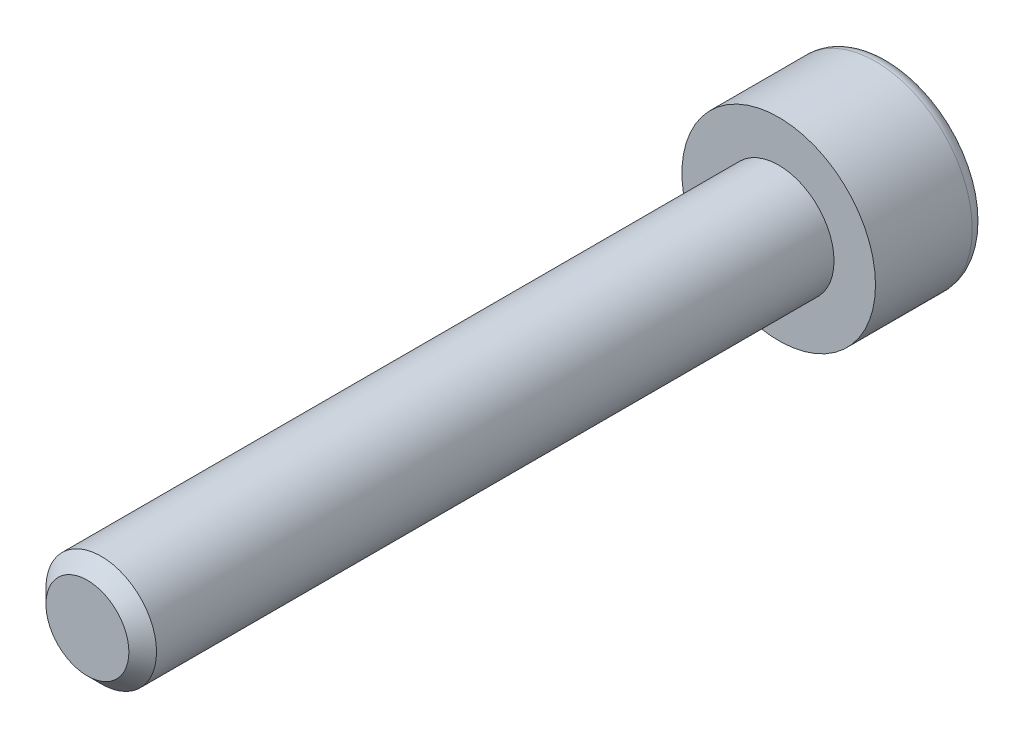
SolidWorks part; units mm, degrees
ref_plane "Plan de face" through (0, 0, 0) normal (0, 0, 1) x (1, 0, 0)
ref_plane "Plan de dessus" through (0, 0, 0) normal (0, 1, 0) x (1, 0, 0)
ref_plane "Plan de droite" through (0, 0, 0) normal (1, 0, 0) x (0, 0, -1)
sketch "Esquisse1" plane through (0, 0, 0) normal (0, 0, 1) x (1, 0, 0)
  circle A0 centre (0, 0) radius 3.5
  dimension "D1" = 7
extrude "Boss.-Extru.1" add sketch "Esquisse1" along normal blind 4
sketch "Esquisse2" plane through (0, 0, 4) normal (0, 0, 1) x (1, 0, 0)
  circle A0 centre (0, 0) radius 2
  dimension "D1" = 4
extrude "Boss.-Extru.2" add sketch "Esquisse2" along normal blind 25
sketch "Esquisse3" plane through (0, 0, 0) normal (0, 0, -1) x (-1, 0, 0)
  line L1 (1.7321, 0) -> (0.866, 1.5)
  line L2 (0.866, 1.5) -> (-0.866, 1.5)
  line L3 (-0.866, 1.5) -> (-1.7321, 0)
  line L4 (-1.7321, 0) -> (-0.866, -1.5)
  line L5 (-0.866, -1.5) -> (0.866, -1.5)
  line L6 (0.866, -1.5) -> (1.7321, 0)
  circle A0 centre (0, 0) radius 1.5 construction
  dimension "D1" = 3
extrude "Enlèv. mat.-Extru.1" cut sketch "Esquisse3" against normal blind 3
chamfer "Chanfrein1" distance 0.5 angle 45 1 edges at (2, 0, 29)
fillet "Congé1" radius 0.5 1 edges at (3.5, 0, 0)
